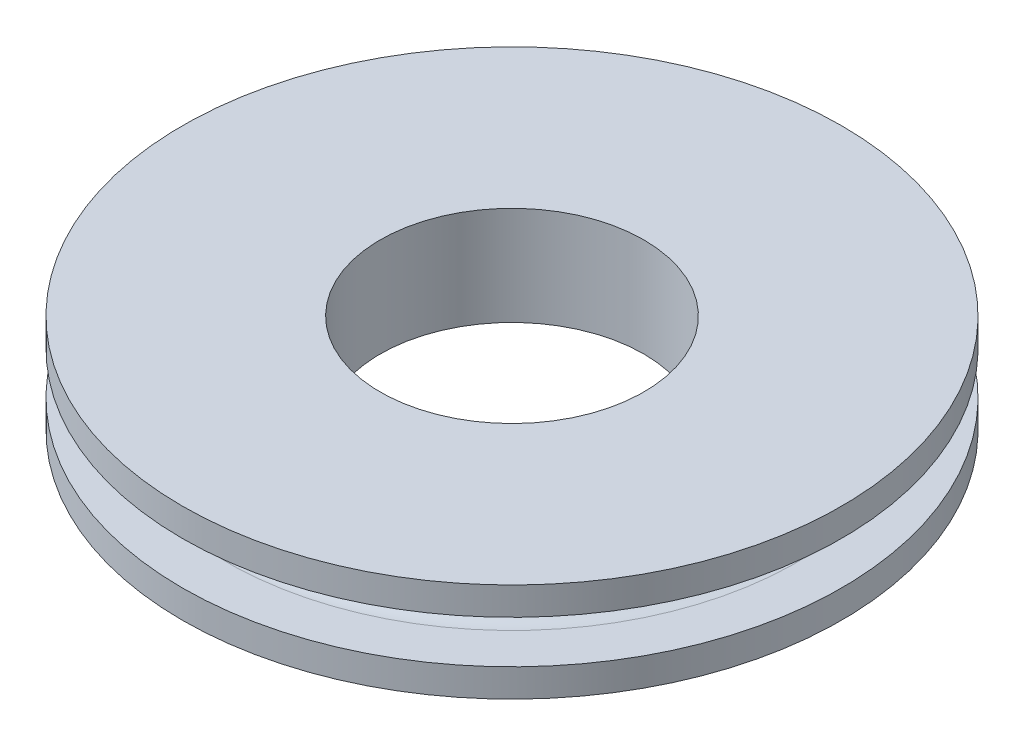
SolidWorks part; units mm, degrees
ref_plane "Front Plane" through (0, 0, 0) normal (0, 0, 1) x (1, 0, 0)
ref_plane "Top Plane" through (0, 0, 0) normal (0, 1, 0) x (1, 0, 0)
ref_plane "Right Plane" through (0, 0, 0) normal (1, 0, 0) x (0, 0, -1)
sketch "Sketch1" plane through (0, 0, 0) normal (0, 0, 1) x (1, 0, 0)
  line L0 (0, -1.5) -> (0, 1.5) construction
  line L1 (0, 1.5) -> (8.65, 1.5) construction
  line L2 (8.65, 1.5) -> (8.65, -1.5) construction
  line L3 (8.65, -1.5) -> (0, -1.5) construction
  line L4 (4, 1.5) -> (4, -1.5)
  line L5 (4, 0.65) -> (8.65, 0.65) construction
  line L6 (4, -0.65) -> (8.65, -0.65) construction
  line L7 (8.65, -0.65) -> (8.65, -1.5) construction
  line L8 (8.65, -1.5) -> (4, -1.5)
  line L9 (4, 1.5) -> (8.65, 1.5)
  line L10 (8.65, 1.5) -> (8.65, 0.65) construction
  line L11 (4, 0) -> (8, 0) construction
  line L12 (8.65, 1.5) -> (10, 1.5)
  line L13 (10, 1.5) -> (10, 0.65)
  line L14 (10, 0.65) -> (8.65, 0.65)
  line L15 (8.65, -0.65) -> (10, -0.65)
  line L16 (10, -0.65) -> (10, -1.5)
  line L17 (10, -1.5) -> (8.65, -1.5)
  line L18 (8.65, 0) -> (8.5, 0) construction
  arc A0 (8.65, 0.65) -> (8.65, -0.65) centre (8.65, 0) ccw
  circle A1 centre (8.5, 0) radius 0.5 construction
  point P4 (0, 0)
  dimension "D2" = 8
  dimension "D3" = 1.3
  dimension "D5" = 1
  dimension "D6" = 1
  dimension "D1" = 4
  dimension "D4" = 3
revolve "Revolve1" add sketch "Sketch1" angle 360 about L0
